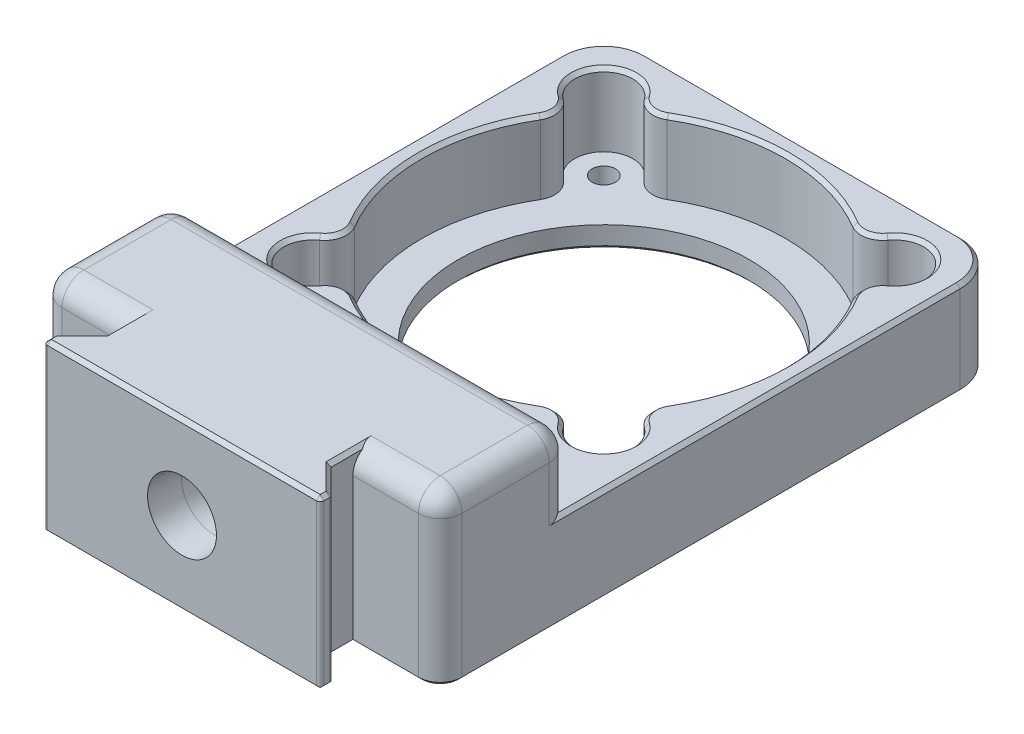
SolidWorks part; units mm, degrees
ref_plane "Front Plane" through (0, 0, 0) normal (0, 0, 1) x (1, 0, 0)
ref_plane "Top Plane" through (0, 0, 0) normal (0, 1, 0) x (1, 0, 0)
ref_plane "Right Plane" through (0, 0, 0) normal (1, 0, 0) x (0, 0, -1)
sketch "MountingPattern" plane through (0, 0, 0) normal (0, 1, 0) x (1, 0, 0)
  line L1 (-20, -20) -> (20, -20) construction
  line L2 (-20, -20) -> (-20, 20) construction
  line L3 (-20, 20) -> (20, 20) construction
  line L4 (20, -20) -> (20, 20) construction
  line L5 (-20, -20) -> (20, 20) construction
  line L6 (-20, 20) -> (20, -20) construction
  circle A0 centre (-20, 20) radius 1.75
  circle A1 centre (20, 20) radius 1.75
  circle A2 centre (20, -20) radius 1.75
  circle A3 centre (-20, -20) radius 1.75
  point P0 (0, 0)
  dimension "D1" = 3.5
  dimension "D2" = 40
sketch "CameraBody" plane through (0, 0, 0) normal (0, 1, 0) x (1, 0, 0)
  line L0 (-20, 20) -> (20, 20) construction
  line L1 (-23.75, 22.1844) -> (23.75, 22.1844) construction
  line L2 (-23.75, 22.1844) -> (-23.75, -47.818) construction
  line L3 (-23.75, -47.818) -> (23.75, -47.818) construction
  line L4 (23.75, 22.1844) -> (23.75, -47.818) construction
  point P0 (0, 22.1844)
  dimension "D1" = 47.5
  dimension "D2" = 70.0024
  dimension "D3" = 2.1844
sketch "Sketch3" plane through (0, 0, 0) normal (0, 1, 0) x (1, 0, 0)
  line L0 (27.5, 20) -> (20, 20) construction
  line L1 (-27.5, 27.5) -> (27.5, 27.5)
  line L2 (-27.5, 27.5) -> (-27.5, -50)
  line L3 (-27.5, -50) -> (27.5, -50)
  line L4 (27.5, 27.5) -> (27.5, -50)
  line L5 (20, 20) -> (20, 27.5) construction
  circle A0 centre (0, 0) radius 20
  circle A21 centre (-20, 20) radius 1.6
  circle A22 centre (20, 20) radius 1.6
  circle A23 centre (20, -20) radius 1.6
  circle A24 centre (-20, -20) radius 1.6
  point P7 (0, 27.5)
  dimension "D1" = 40
  dimension "D3" = 3.2
  dimension "D2" = 55
  dimension "D4" = 50
extrude "MountingFlange" add sketch "Sketch3" along normal blind 3
sketch "Sketch4" plane through (0, 3, 0) normal (0, 1, 0) x (1, 0, 0)
  line L0 (27.5, 27.5) -> (-27.5, 27.5) construction
  line L1 (-27.5, -50) -> (27.5, -50) construction
  line L2 (27.5, -50) -> (27.5, 27.5) construction
  line L3 (-27.5, 27.5) -> (-27.5, -50) construction
  line L4 (-27.5, -50) -> (27.5, -50)
  line L5 (27.5, -50) -> (27.5, 27.5)
  line L6 (-27.5, 27.5) -> (-27.5, -50)
  line L7 (27.5, 27.5) -> (-27.5, 27.5)
  circle A0 centre (0, 0) radius 25
  dimension "D1" = 50
extrude "PictureFrame" add sketch "Sketch4" along normal blind 10
sketch "Sketch5" plane through (0, 3, 0) normal (0, -1, 0) x (1, 0, 0)
  circle A0 centre (20, -20) radius 4
  circle A1 centre (-20, -20) radius 4
  circle A2 centre (-20, 20) radius 4
  circle A3 centre (20, 20) radius 4
  dimension "D1" = 8
extrude "ScrewCounterbore" cut sketch "Sketch5" against normal through all
fillet "FilletScrewCounterbore" radius 3 8 edges at (19.129, 8, -16.096) (16.096, 8, -19.129) (-19.129, 8, 16.096) (-16.096, 8, 19.129) (16.096, 8, 19.129) (19.129, 8, 16.096) (-16.096, 8, -19.129) (-19.129, 8, -16.096)
fillet "FilletOuterCorners" radius 6 2 edges at (27.5, 6.5, -27.5) (-27.5, 6.5, -27.5)
sketch "Sketch6" plane through (0, 13, 0) normal (0, 1, 0) x (1, 0, 0)
  line L0 (27.5, -50) -> (27.5, 21.5) construction
  line L1 (-27.5, -50) -> (27.5, -50)
  line L2 (-27.5, -50) -> (-27.5, -32)
  line L3 (-27.5, -32) -> (27.5, -32)
  line L4 (27.5, -50) -> (27.5, -32)
  dimension "D1" = 32
extrude "Base" add sketch "Sketch6" along normal blind 10
sketch "Sketch8" plane through (0, 23, 0) normal (0, 1, 0) x (1, 0, 0)
  line L0 (-15.5, -53) -> (-19, -56.5)
  line L3 (19, -56.5) -> (15.5, -53)
  line L5 (19, -56.5) -> (19, -58)
  line L6 (19, -58) -> (-19, -58)
  line L7 (-19, -58) -> (-19, -56.5)
  line L8 (-15.5, -53) -> (-15.5, -50)
  line L9 (-27.5, -50) -> (27.5, -50) construction
  line L10 (-15.5, -50) -> (15.5, -50)
  line L11 (15.5, -50) -> (15.5, -53)
  point P2 (0, -50)
  dimension "D1" = 38
  dimension "D2" = 45
  dimension "D3" = 3.5
  dimension "D4" = 1.5
  dimension "D5" = 3
extrude "ArcaBase" add sketch "Sketch8" against normal up to surface (23 mm away) up to face at (0, 0, -0.0809)
sketch "Sketch7" plane through (0, 0, 58) normal (0, 0, 1) x (1, 0, 0)
  line L0 (-27.5, 23) -> (-27.5, 0) construction
  circle A0 centre (0, 11.5) radius 4.4323
  point P5 (-27.5, 11.5)
  dimension "D1" = 8.8646
extrude "TripodMount" cut sketch "Sketch7" against normal blind 12
fillet "FilletLarge" radius 3 9 edges at (-27.5, 18, 32) (27.5, 18, 32) (-27.5, 23, 41) (-21.5, 23, 50) (27.5, 23, 41) (0, 23, 32) (21.5, 23, 50) (27.5, 11.5, 50) (-27.5, 11.5, 50)
chamfer "ChamferBottom" distance 0.5 angle 45 21 edges at (0, 0, 20) (0, 0, -27.5) (-27.5, 0, 12.75) (-25.7426, 0, -25.7426) (25.7426, 0, -25.7426) (20, 0, -18.4) (20, 0, 50) (-15.5, 0, 51.5) (15.5, 0, 51.5) (17.25, 0, 54.75) (19, 0, 57.25) (0, 0, 58) (-19, 0, 57.25) (-17.25, 0, 54.75) (20, 0, 21.6) (27.5, 0, 12.75) (-20, 0, 50) (-26.6213, 0, 49.1213) (26.6213, 0, 49.1213) (-20, 0, 21.6) (-20, 0, -18.4)
chamfer "ChamferTop" distance 0.5 angle 45 21 edges at (27.5, 13, 6.75) (-27.5, 13, 6.75) (25.7426, 13, -25.7426) (-25.7426, 13, -25.7426) (0, 13, -27.5) (0, 13, 25) (14.9216, 13, 21.1342) (-14.9216, 13, 21.1342) (22.8284, 13, 22.8284) (-22.8284, 13, 22.8284) (21.1342, 13, 14.9216) (-21.1342, 13, 14.9216) (25, 13, 0) (-25, 13, 0) (21.1342, 13, -14.9216) (-21.1342, 13, -14.9216) (22.8284, 13, -22.8284) (-22.8284, 13, -22.8284) (14.9216, 13, -21.1342) (-14.9216, 13, -21.1342) (0, 13, -25)
chamfer "ChamferTripodMount" distance 0.3048 angle 86 1 edges at (4.4323, 11.5, 58)
fillet "FilletArcaBase" radius 0.5 4 edges at (19, 11.75, 58) (19, 11.75, 56.5) (-19, 11.75, 56.5) (-19, 11.75, 58)
chamfer "Chamfer1" distance 0.5 angle 45 11 edges at (-15.5, 23, 50) (-17.1768, 23, 54.6768) (-18.9619, 23, 56.5158) (-19, 23, 57.1036) (-18.8536, 23, 57.8536) (15.5, 23, 50) (17.1768, 23, 54.6768) (18.9619, 23, 56.5158) (19, 23, 57.1036) (18.8536, 23, 57.8536) (0, 23, 58)
